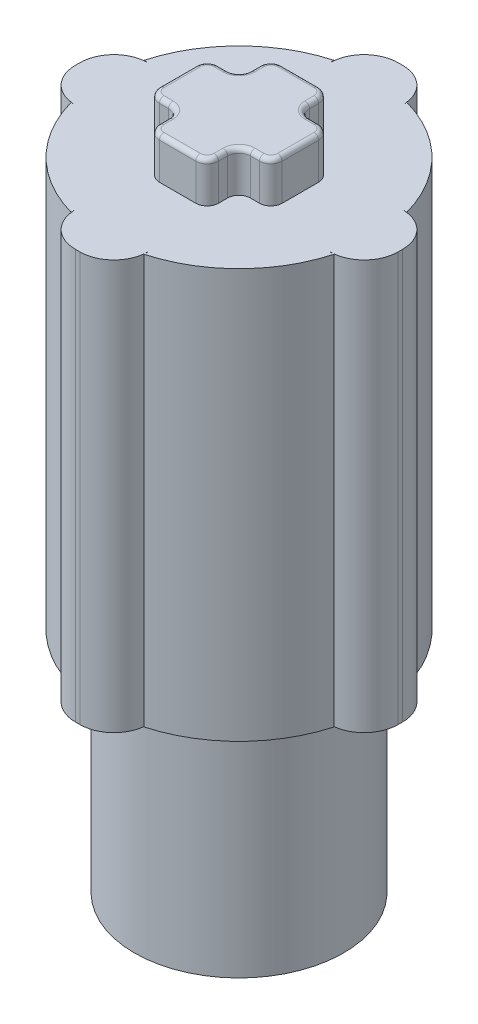
SolidWorks part; units mm, degrees
material "ABS"
ref_plane "Front Plane" through (0, 0, 0) normal (0, 0, 1) x (1, 0, 0)
ref_plane "Top Plane" through (0, 0, 0) normal (0, 1, 0) x (1, 0, 0)
ref_plane "Right Plane" through (0, 0, 0) normal (1, 0, 0) x (0, 0, -1)
sketch "Sketch1" plane through (0, 0, 0) normal (0, 1, 0) x (1, 0, 0)
  circle A0 centre (0, 0) radius 2.3
  dimension "D1" = 4.6
extrude "Boss-Extrude1" add sketch "Sketch1" along normal blind 5
sketch "Sketch2" plane through (0, 5, 0) normal (0, 1, 0) x (1, 0, 0)
  line L0 (-3.55, 0) -> (3.55, 0) construction
  line L1 (0.05, 3.55) -> (-0.05, 3.55)
  line L2 (0.8, 2.8) -> (0.8, 2.8914)
  line L3 (0.05, -3.55) -> (-0.05, -3.55)
  line L4 (-0.8, 2.8) -> (-0.8, 2.8914)
  line L5 (-2.8, 0.8) -> (-2.8914, 0.8)
  line L6 (-3.55, 0.05) -> (-3.55, -0.05)
  line L7 (-2.8, -0.8) -> (-2.8914, -0.8)
  line L8 (3.55, 0.05) -> (3.55, -0.05)
  line L9 (0, 3.55) -> (0, -3.55) construction
  line L10 (-0.8, -2.8914) -> (-0.8, -2.8)
  line L12 (2.8914, 0.8) -> (2.8, 0.8)
  line L13 (2.8914, -0.8) -> (2.8, -0.8)
  line L14 (0.8, -2.8914) -> (0.8, -2.8)
  line L15 (-0.8, 2.8) -> (-0.05, 2.8) construction
  line L16 (-0.05, 2.8) -> (0.05, 2.8) construction
  line L17 (0.05, 2.8) -> (0.8, 2.8) construction
  line L18 (-0.05, 3.55) -> (-0.05, 2.8) construction
  line L19 (-0.05, 2.8) -> (-0.05, -2.8) construction
  line L20 (-0.05, -2.8) -> (-0.05, -3.55) construction
  line L21 (0.05, -3.55) -> (0.05, -2.8) construction
  line L22 (0.05, -2.8) -> (0.05, 2.8) construction
  line L23 (0.05, 2.8) -> (0.05, 3.55) construction
  line L24 (-0.8, -2.8) -> (-0.05, -2.8) construction
  line L25 (-0.05, -2.8) -> (0.05, -2.8) construction
  line L26 (0.05, -2.8) -> (0.8, -2.8) construction
  arc A0 (-0.8, 2.8914) -> (-2.8914, 0.8) centre (0, 0) ccw
  arc A1 (0.8, -2.8) -> (0.05, -3.55) centre (0.05, -2.8) cw
  arc A2 (-0.05, -3.55) -> (-0.8, -2.8) centre (-0.05, -2.8) cw
  arc A3 (-0.05, 3.55) -> (-0.8, 2.8) centre (-0.05, 2.8) ccw
  arc A4 (0.05, 3.55) -> (0.8, 2.8) centre (0.05, 2.8) cw
  arc A5 (2.8, 0.8) -> (3.55, 0.05) centre (2.8, 0.05) cw
  arc A6 (2.8, -0.8) -> (3.55, -0.05) centre (2.8, -0.05) ccw
  arc A7 (-3.55, -0.05) -> (-2.8, -0.8) centre (-2.8, -0.05) ccw
  arc A8 (-2.8, 0.8) -> (-3.55, 0.05) centre (-2.8, 0.05) ccw
  arc A9 (-2.8914, -0.8) -> (-0.8, -2.8914) centre (0, 0) ccw
  arc A10 (2.8914, 0.8) -> (0.8, 2.8914) centre (0, 0) ccw
  arc A11 (0.8, -2.8914) -> (2.8914, -0.8) centre (0, 0) ccw
  point P15 (0, 0)
  point P16 (0, 0)
  point P27 (3.55, 0.8)
  point P32 (-3.55, -0.8)
  point P35 (-3.55, 0.8)
  dimension "D1" = 6
  dimension "D4" = 0.75
  dimension "D2" = 7.1
  dimension "D3" = 1.6
extrude "Boss-Extrude2" add sketch "Sketch2" along normal blind 9
sketch "Sketch3" plane through (0, 14, 0) normal (0, 1, 0) x (1, 0, 0)
  line L0 (0, 1.35) -> (0, -1.35) construction
  line L1 (-0.4, 1.35) -> (0.4, 1.35)
  line L2 (-0.65, 1.1) -> (-0.65, 0.9)
  line L3 (-0.4, -1.35) -> (0.4, -1.35)
  line L4 (0.65, 1.1) -> (0.65, 0.9)
  line L5 (-1.1, 0.65) -> (-0.9, 0.65)
  line L6 (-1.35, 0.4) -> (-1.35, -0.4)
  line L7 (-1.1, -0.65) -> (-0.9, -0.65)
  line L8 (1.35, 0.4) -> (1.35, -0.4)
  line L9 (-1.35, 0) -> (1.35, 0) construction
  line L10 (-0.65, -0.9) -> (-0.65, -1.1)
  line L11 (0.9, 0.65) -> (1.1, 0.65)
  line L12 (0.65, -0.9) -> (0.65, -1.1)
  line L13 (0.9, -0.65) -> (1.1, -0.65)
  arc A0 (0.65, -0.9) -> (0.9, -0.65) centre (0.9, -0.9) cw
  arc A1 (-0.65, -0.9) -> (-0.9, -0.65) centre (-0.9, -0.9) ccw
  arc A2 (0.9, 0.65) -> (0.65, 0.9) centre (0.9, 0.9) cw
  arc A3 (-0.65, 0.9) -> (-0.9, 0.65) centre (-0.9, 0.9) cw
  arc A4 (-0.4, 1.35) -> (-0.65, 1.1) centre (-0.4, 1.1) ccw
  arc A5 (0.4, 1.35) -> (0.65, 1.1) centre (0.4, 1.1) cw
  arc A6 (1.1, 0.65) -> (1.35, 0.4) centre (1.1, 0.4) cw
  arc A7 (1.1, -0.65) -> (1.35, -0.4) centre (1.1, -0.4) ccw
  arc A8 (0.4, -1.35) -> (0.65, -1.1) centre (0.4, -1.1) ccw
  arc A9 (-0.65, -1.1) -> (-0.4, -1.35) centre (-0.4, -1.1) ccw
  arc A10 (-1.35, -0.4) -> (-1.1, -0.65) centre (-1.1, -0.4) ccw
  arc A11 (-1.1, 0.65) -> (-1.35, 0.4) centre (-1.1, 0.4) ccw
  point P12 (0, 0)
  point P14 (0, 0)
  point P21 (0.65, -0.65)
  point P34 (1.35, 0.65)
  point P43 (-1.35, -0.65)
  point P46 (-1.35, 0.65)
  dimension "D3" = 0.25
  dimension "D1" = 1.3
  dimension "D2" = 2.7
extrude "Boss-Extrude3" add sketch "Sketch3" along normal blind 0.9
fillet "Fillet2" radius 0.1 24 edges at (-0.5768, 14.9, 1.2768) (-0.65, 14.9, 1) (-0.7232, 14.9, 0.7232) (-1, 14.9, 0.65) (-1.2768, 14.9, 0.5768) (-1.35, 14.9, 0) (-1.2768, 14.9, -0.5768) (-1, 14.9, -0.65) (-0.7232, 14.9, -0.7232) (-0.65, 14.9, -1) (-0.5768, 14.9, -1.2768) (0, 14.9, -1.35) (0.5768, 14.9, -1.2768) (0.65, 14.9, -1) (0.7232, 14.9, -0.7232) (1, 14.9, -0.65) (1.2768, 14.9, -0.5768) (1.35, 14.9, 0) (1.2768, 14.9, 0.5768) (1, 14.9, 0.65) (0.7232, 14.9, 0.7232) (0.65, 14.9, 1) (0.5768, 14.9, 1.2768) (0, 14.9, 1.35)
